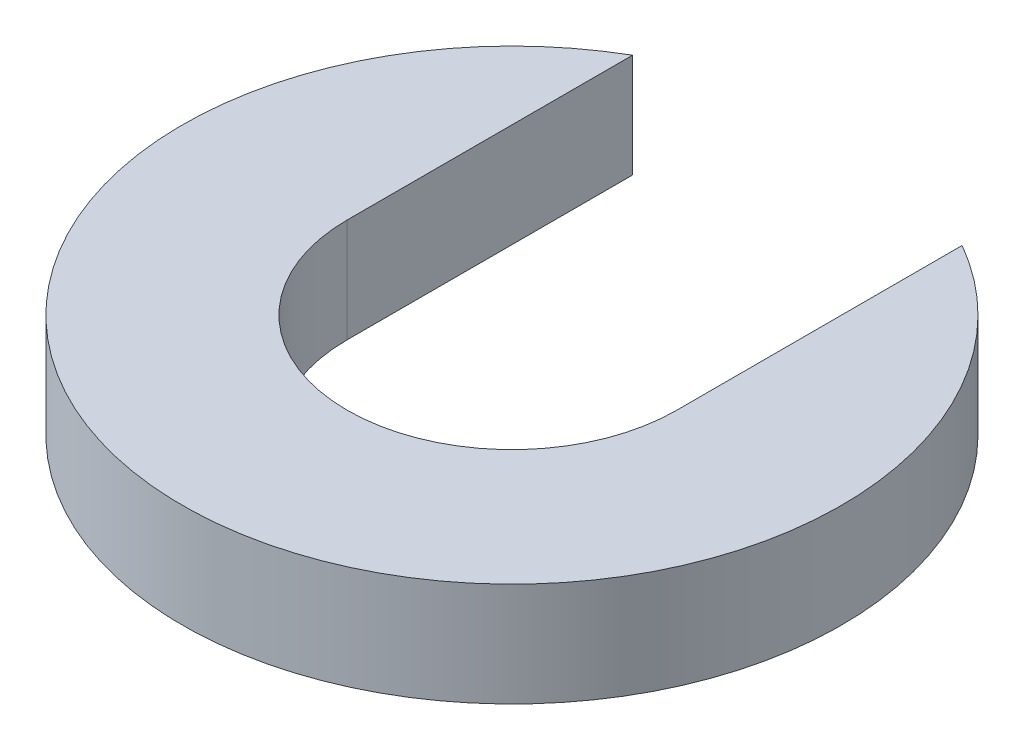
SolidWorks part; units mm, degrees
ref_plane "Front Plane" through (0, 0, 0) normal (0, 0, 1) x (1, 0, 0)
ref_plane "Top Plane" through (0, 0, 0) normal (0, 1, 0) x (1, 0, 0)
ref_plane "Right Plane" through (0, 0, 0) normal (1, 0, 0) x (0, 0, -1)
sketch "Sketch1" plane through (0, 0, 0) normal (0, 1, 0) x (1, 0, 0)
  line L0 (-4.7625, 0) -> (-4.7625, 8.2489)
  line L1 (4.7625, 0) -> (4.7625, 8.2489)
  circle A0 centre (0, 0) radius 9.525
  circle A1 centre (0, 0) radius 4.7625
  dimension "D1" = 19.05
  dimension "D2" = 9.525
extrude "Boss-Extrude1" add sketch "Sketch1" along normal blind 3 contours A1 L0 A0 L1
